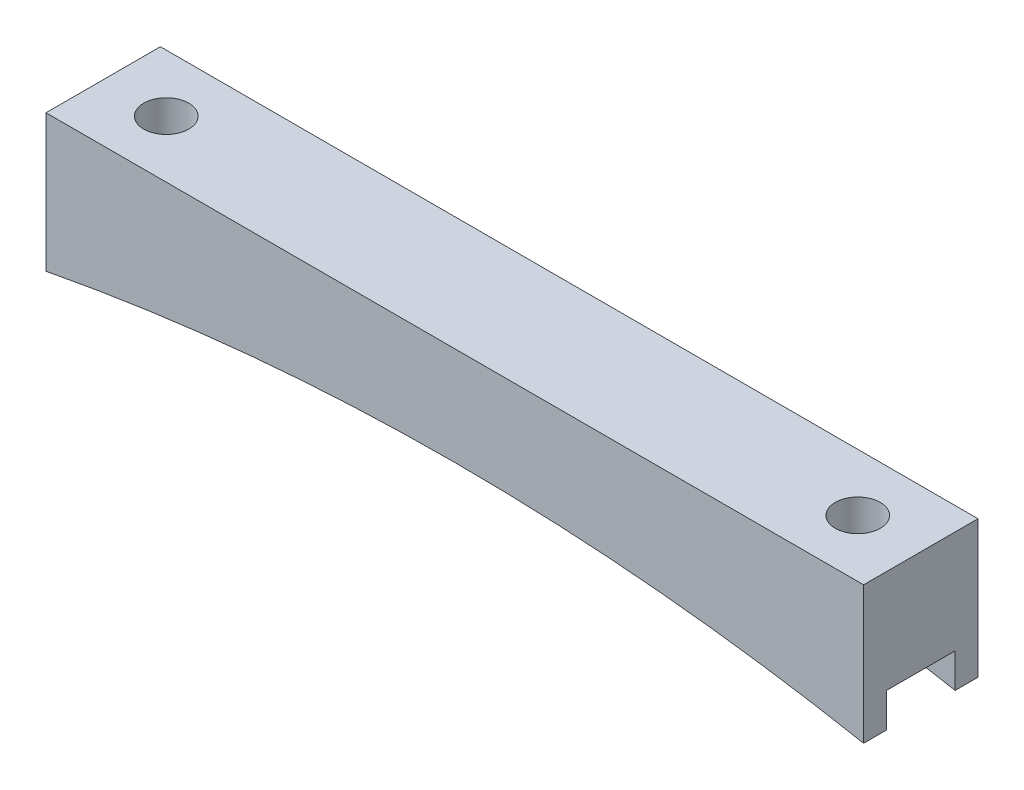
SolidWorks part; units mm, degrees
ref_plane "Front Plane" through (0, 0, 0) normal (0, 0, 1) x (1, 0, 0)
ref_plane "Top Plane" through (0, 0, 0) normal (0, 1, 0) x (1, 0, 0)
ref_plane "Right Plane" through (0, 0, 0) normal (1, 0, 0) x (0, 0, -1)
sketch "Sketch1" plane through (0, 0, 0) normal (0, 0, 1) x (1, 0, 0)
  line L0 (-45.385, 0) -> (45.385, 0)
  line L1 (-38.385, -2.54) -> (38.385, -2.54) construction
  line L2 (0, 0) -> (0, -4.6068) construction
  line L3 (45.385, 0) -> (45.385, -15.24)
  line L4 (-45.385, 0) -> (-45.385, -15.24)
  arc A0 (-45.385, -15.24) -> (45.385, -15.24) centre (0, -252.2334) cw
  point P4 (0, 0)
  point P9 (0, -2.54)
  dimension "D4" = 241.3
  dimension "D1" = 76.77
  dimension "D2" = 2.54
  dimension "D3" = 7
  dimension "D5" = 15.24
extrude "Boss-Extrude1" add sketch "Sketch1" along normal blind 12.7
sketch "Sketch2" plane through (0, 0, 0) normal (0, 1, 0) x (1, 0, 0)
  line L1 (-38.385, 0) -> (-38.385, -12.7) construction
  line L2 (-45.385, 0) -> (45.385, 0) construction
  line L3 (45.385, -12.7) -> (-45.385, -12.7) construction
  line L4 (38.385, 0) -> (38.385, -12.7) construction
  circle A0 centre (-38.385, -6.35) radius 2.5
  circle A1 centre (38.385, -6.35) radius 2.5
  circle A2 centre (-38.385, -6.35) radius 3 construction
  point P7 (-38.385, -6.35)
  dimension "D1" = 5
  dimension "D2" = 6
extrude "Cut-Extrude1" cut sketch "Sketch2" against normal through all
sketch "Sketch3" plane through (45.385, 0, 0) normal (1, 0, 0) x (0, 0, -1)
  line L0 (-12.7, -15.24) -> (0, -15.24) construction
  line L1 (-10.16, -15.24) -> (-2.54, -15.24)
  line L2 (-10.16, -15.24) -> (-10.16, -11.43)
  line L3 (-10.16, -11.43) -> (-2.54, -11.43)
  line L4 (-2.54, -15.24) -> (-2.54, -11.43)
  line L5 (-12.7, -15.24) -> (-12.7, 0) construction
  line L6 (0, -15.24) -> (0, 0) construction
  dimension "D1" = 2.54
  dimension "D2" = 2.54
  dimension "D3" = 3.81
extrude "Cut-Extrude2" cut sketch "Sketch3" against normal through all
